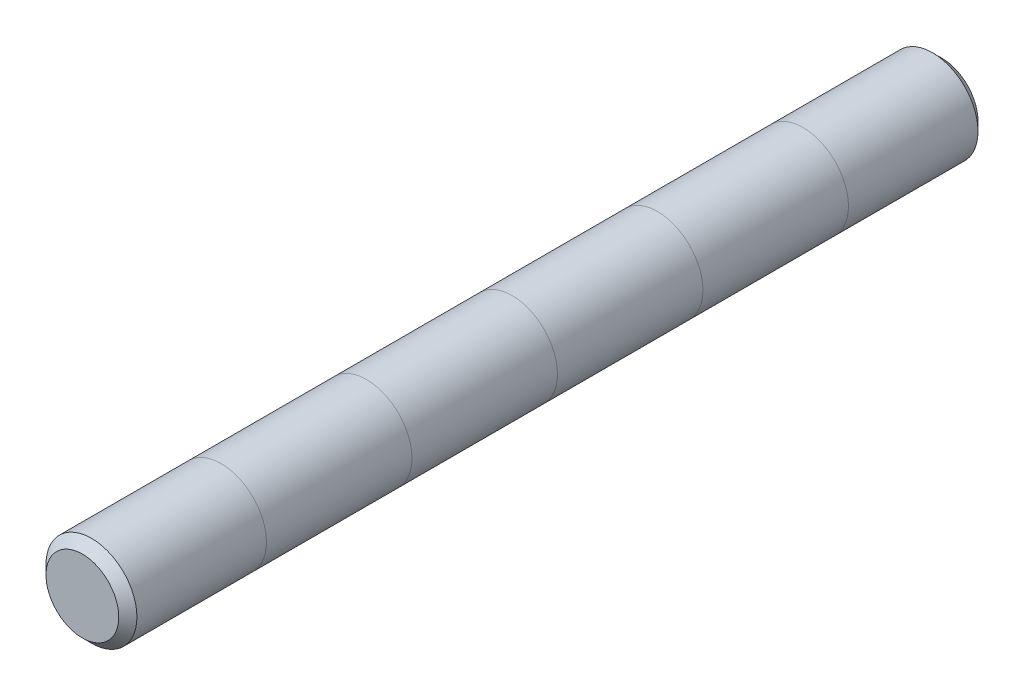
SolidWorks part; units mm, degrees
material "Plain Carbon Steel"
ref_plane "Front" through (0, 0, 0) normal (0, 0, 1) x (1, 0, 0)
ref_plane "Top" through (0, 0, 0) normal (0, 1, 0) x (1, 0, 0)
ref_plane "Right" through (0, 0, 0) normal (1, 0, 0) x (0, 0, -1)
sketch "Sketch1" plane through (0, 0, 0) normal (0, 0, 1) x (1, 0, 0)
  circle A0 centre (0, 0) radius 7.9375
  dimension "Diameter" = 15.875
sketch "Sketch2" plane through (0, 0, 0) normal (1, 0, 0) x (0, 0, -1)
  line L0 (-75, 0) -> (75, 0) construction
  line L1 (-24.2, 7.9375) -> (-24.2, -7.9375) construction
  line L2 (55, 0) -> (-55, 0) construction
  line L3 (24.2, 7.9375) -> (24.2, -7.9375) construction
  line L4 (-75, 7.9375) -> (-75, -7.9375) construction
  line L5 (75, 7.9375) -> (75, -7.9375) construction
  point P3 (-24.2, 0)
  point P8 (0, 0)
  point P9 (24.2, 0)
  point P15 (-75, 0)
  point P18 (75, 0)
  dimension "D1" = 15.875
  dimension "Length" = 150
  dimension "D2" = 50.8
  dimension "D3" = 50.8
sketch "Sketch3" plane through (0, 0, 0) normal (0, 0, 1) x (1, 0, 0)
  circle A0 centre (0, 0) radius 7.9375
  dimension "D1" = 15.875
extrude "Boss-Extrude1" add sketch "Sketch3" along normal mid plane 150
chamfer "Chamfer1" distance 1.5875 angle 45 2 edges at (7.9375, 0, -75) (7.9375, 0, 75)
sketch "Sketch4" plane through (0, 0, 0) normal (1, 0, 0) x (0, 0, -1)
  line L0 (-25.4, 7.9375) -> (-25.4, -7.9375)
  line L1 (73.4125, 7.9375) -> (-73.4125, 7.9375) construction
  line L2 (-73.4125, -7.9375) -> (73.4125, -7.9375) construction
  line L3 (0, 7.9375) -> (0, -7.9375)
  line L5 (25.4, 7.9375) -> (25.4, -7.9375)
  line L6 (50.8, 7.9375) -> (50.8, -7.9375)
  line L7 (-50.8, 7.9375) -> (-50.8, -7.9375)
  dimension "D1" = 25.4
  dimension "D2" = 25.4
  dimension "D3" = 25.4
  dimension "D4" = 25.4
split line "Split Line1"
equation "\"D1@Sketch3\" = \"Diameter@Sketch1\""
equation "\"D1@Boss-Extrude1\" = \"Length@Sketch2\""
equation "\"D1@Chamfer1\" = \"Diameter@Sketch1\" * .1"
equation "\"D1@Sketch2\" = \"Diameter@Sketch1\""
